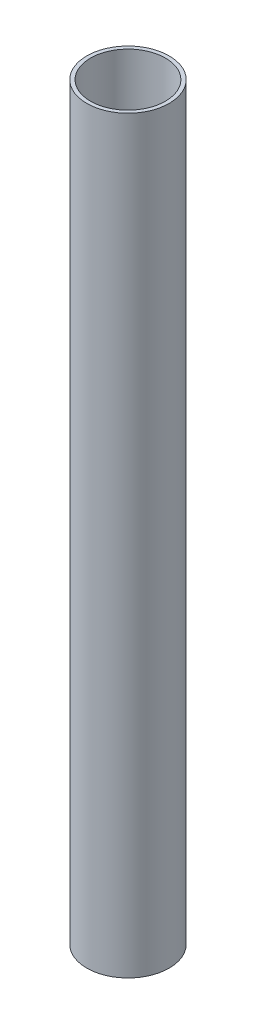
SolidWorks part; units mm, degrees
ref_plane "Front Plane" through (0, 0, 0) normal (0, 0, 1) x (1, 0, 0)
ref_plane "Top Plane" through (0, 0, 0) normal (0, 1, 0) x (1, 0, 0)
ref_plane "Right Plane" through (0, 0, 0) normal (1, 0, 0) x (0, 0, -1)
sketch "Sketch1" plane through (0, 0, 0) normal (0, 1, 0) x (1, 0, 0)
  circle A0 centre (0, 0) radius 55
  circle A1 centre (0, 0) radius 50
  dimension "D1" = 110
  dimension "D2" = 5
extrude "Boss-Extrude1" add sketch "Sketch1" along normal blind 1000
